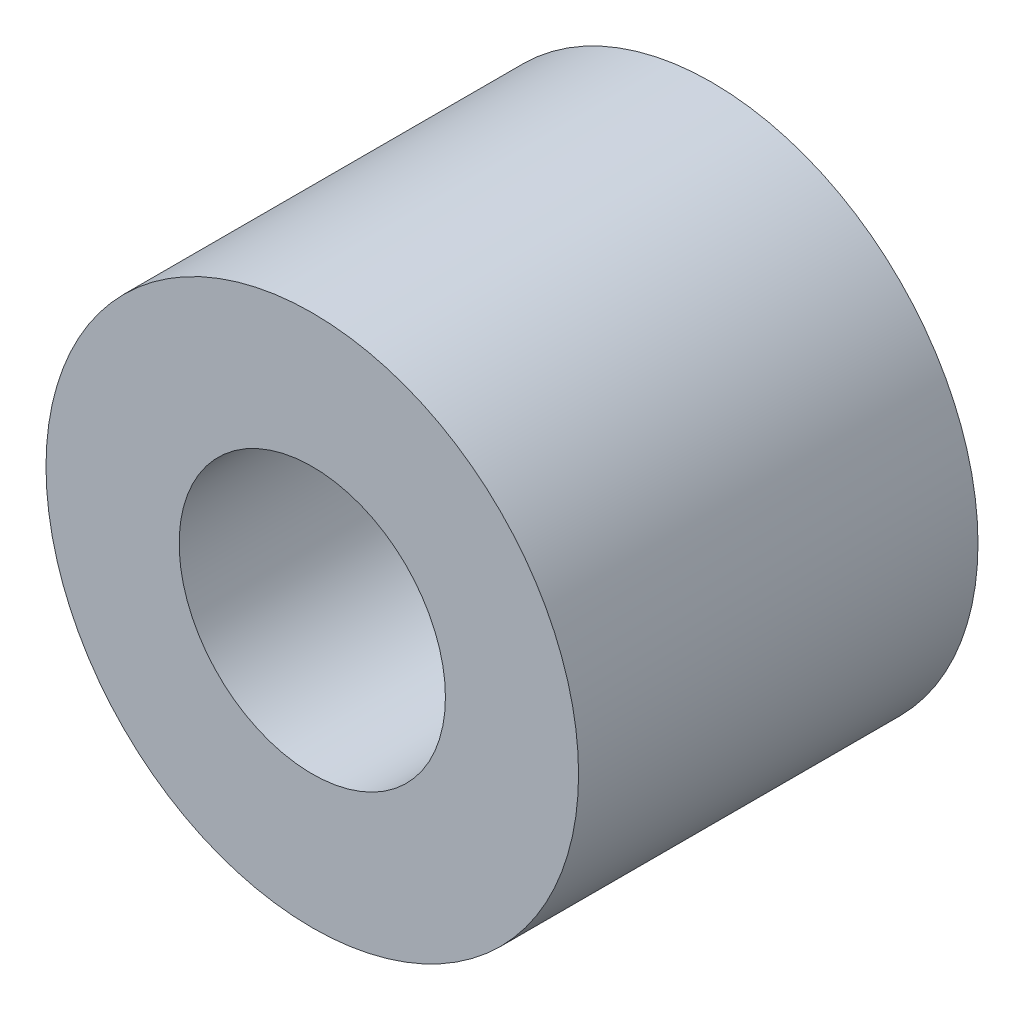
SolidWorks part; units mm, degrees
material "AISI 316 Annealed Stainless Steel Bar (SS)"
ref_plane "Front Plane" through (0, 0, 0) normal (0, 0, 1) x (1, 0, 0)
ref_plane "Top Plane" through (0, 0, 0) normal (0, 1, 0) x (1, 0, 0)
ref_plane "Right Plane" through (0, 0, 0) normal (1, 0, 0) x (0, 0, -1)
sketch "Sketch1" plane through (0, 0, 0) normal (0, 0, 1) x (1, 0, 0)
  circle A0 centre (0, 0) radius 5
  circle A1 centre (0, 0) radius 10
  dimension "D1" = 10
  dimension "D2" = 20
extrude "Boss-Extrude1" add sketch "Sketch1" along normal blind 15
